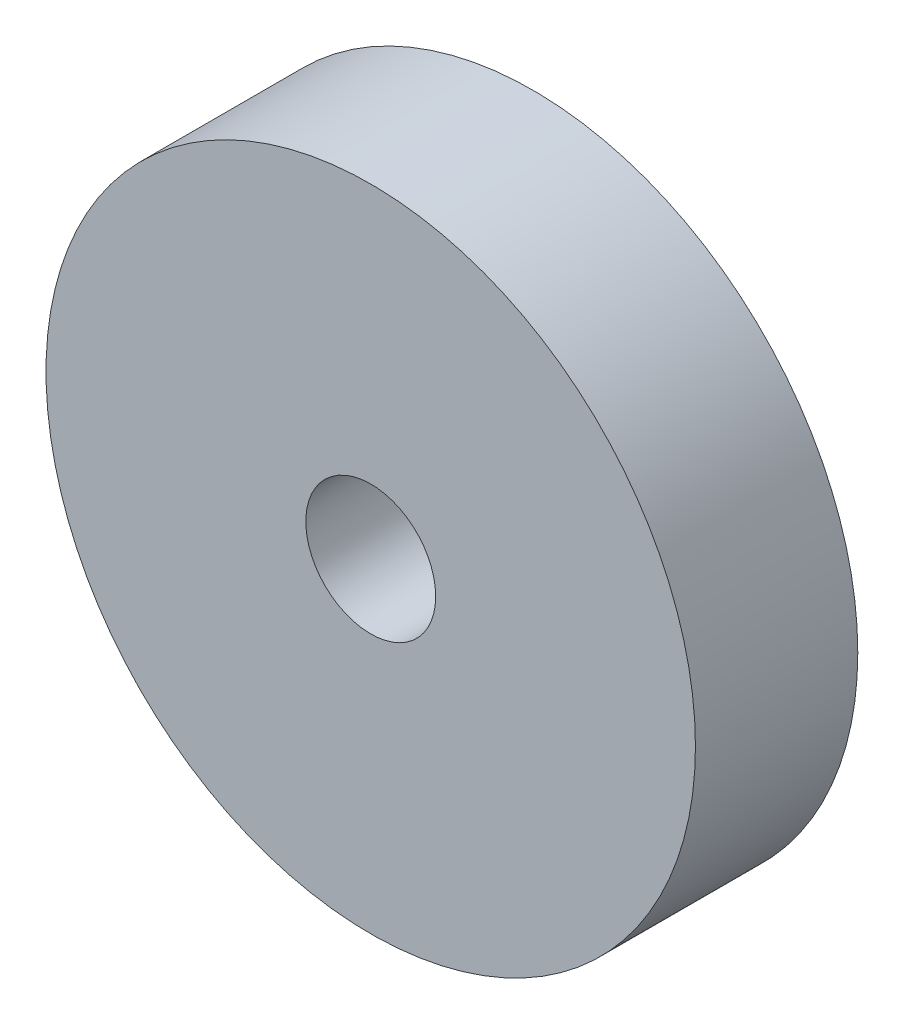
SolidWorks part; units mm, degrees
ref_plane "Front Plane" through (0, 0, 0) normal (0, 0, 1) x (1, 0, 0)
ref_plane "Top Plane" through (0, 0, 0) normal (0, 1, 0) x (1, 0, 0)
ref_plane "Right Plane" through (0, 0, 0) normal (1, 0, 0) x (0, 0, -1)
sketch "Croquis1" plane through (0, 0, 0) normal (0, 0, 1) x (1, 0, 0)
  circle A0 centre (0, 0) radius 0.1
  circle A1 centre (0, 0) radius 0.5
  dimension "D1" = 0.2
  dimension "D2" = 1
extrude "Saliente-Extruir1" add sketch "Croquis1" along normal blind 0.25
